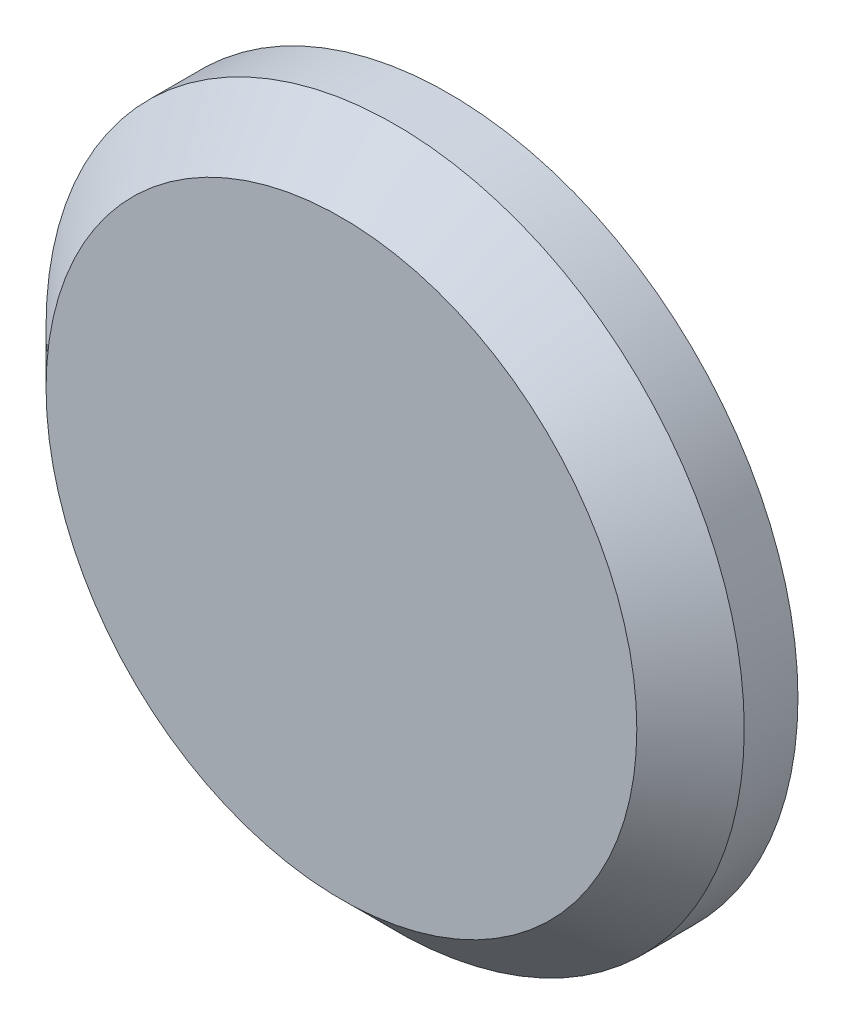
SolidWorks part; units mm, degrees
ref_plane "Front Plane" through (0, 0, 0) normal (0, 0, 1) x (1, 0, 0)
ref_plane "Top Plane" through (0, 0, 0) normal (0, 1, 0) x (1, 0, 0)
ref_plane "Right Plane" through (0, 0, 0) normal (1, 0, 0) x (0, 0, -1)
sketch "Sketch1" plane through (0, 0, 0) normal (0, 0, 1) x (1, 0, 0)
  circle A0 centre (0, 0) radius 3.7
  dimension "D1" = 7.4
extrude "Boss-Extrude1" add sketch "Sketch1" along normal blind 10
sketch "Sketch2" plane through (0, 0, 0) normal (0, 0, -1) x (-1, 0, 0)
  circle A0 centre (0, 0) radius 5
  dimension "D1" = 10
extrude "Boss-Extrude2" add sketch "Sketch2" along normal blind 2
sketch "Sketch3" plane through (0, 0, 10) normal (0, 0, 1) x (1, 0, 0)
  circle A0 centre (0, 0) radius 4.1
  circle A1 centre (0, 0) radius 13
  circle A2 centre (0, 0) radius 3.7 construction
  dimension "D1" = 0.4
  dimension "D2" = 26
extrude "Boss-Extrude3" add sketch "Sketch3" along normal blind 4 separate body
sketch "Sketch4" plane through (0, 0, 10) normal (0, 0, -1) x (-1, 0, 0)
  circle A0 centre (0, 0.4817) radius 21.8873
extrude "Cut-Extrude1" cut sketch "Sketch4" along normal blind 23
chamfer "Chamfer2" distance 2 angle 45 1 edges at (13, 0, 14)
sketch "Sketch5" plane through (0, 0, 14) normal (0, 0, 1) x (1, 0, 0)
  circle A0 centre (0, 0) radius 5.5004
extrude "Boss-Extrude4" add sketch "Sketch5" against normal blind 1
